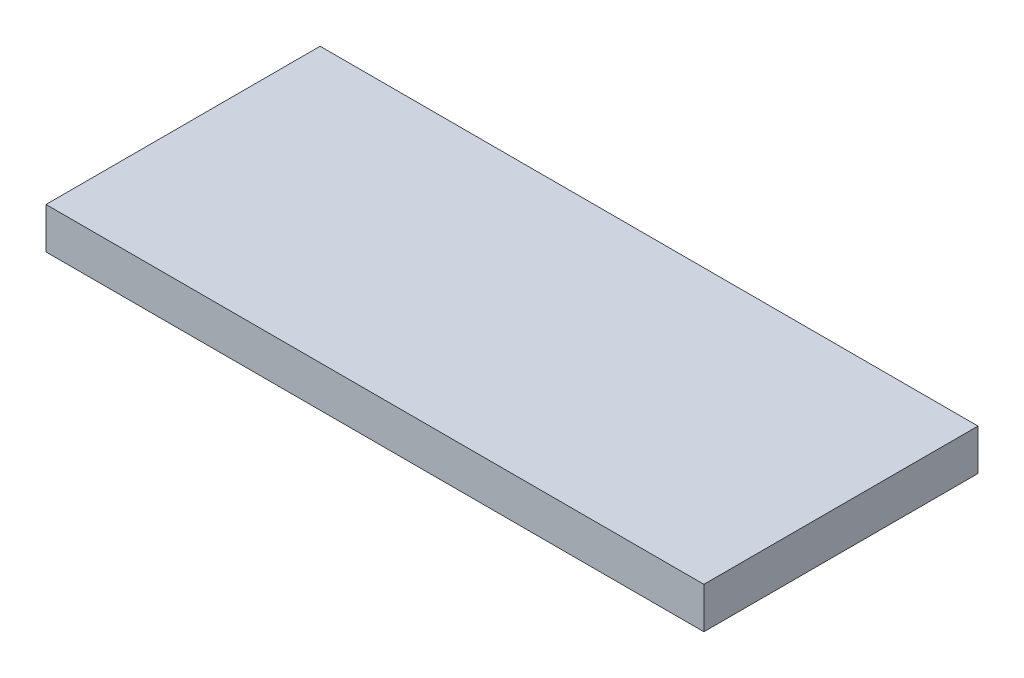
SolidWorks part; units mm, degrees
ref_plane "Front Plane" through (0, 0, 0) normal (0, 0, 1) x (1, 0, 0)
ref_plane "Top Plane" through (0, 0, 0) normal (0, 1, 0) x (1, 0, 0)
ref_plane "Right Plane" through (0, 0, 0) normal (1, 0, 0) x (0, 0, -1)
sketch "Sketch1" plane through (0, 0, 0) normal (0, 1, 0) x (1, 0, 0)
  line L1 (24, -10) -> (-24, -10)
  line L2 (24, -10) -> (24, 10)
  line L3 (24, 10) -> (-24, 10)
  line L4 (-24, -10) -> (-24, 10)
  line L5 (24, -10) -> (-24, 10) construction
  line L6 (24, 10) -> (-24, -10) construction
  point P0 (0, 0)
  dimension "D1" = 48
  dimension "D2" = 20
extrude "Boss-Extrude1" add sketch "Sketch1" along normal blind 3
